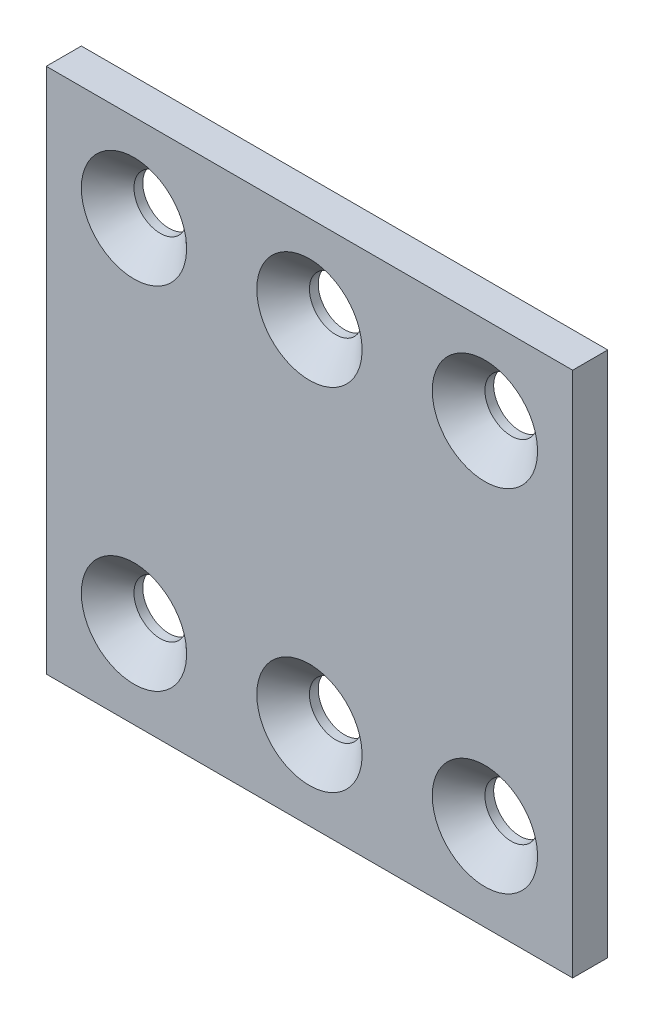
SolidWorks part; units mm, degrees
ref_plane "Front Plane" through (0, 0, 0) normal (0, 0, 1) x (1, 0, 0)
ref_plane "Top Plane" through (0, 0, 0) normal (0, 1, 0) x (1, 0, 0)
ref_plane "Right Plane" through (0, 0, 0) normal (1, 0, 0) x (0, 0, -1)
sketch "Sketch1" plane through (0, 0, 0) normal (0, 0, 1) x (1, 0, 0)
  line L1 (-30, -30) -> (30, -30)
  line L2 (-30, -30) -> (-30, 30)
  line L3 (-30, 30) -> (30, 30)
  line L4 (30, -30) -> (30, 30)
  line L5 (-30, -30) -> (30, 30) construction
  line L6 (-30, 30) -> (30, -30) construction
  point P1 (0, 0)
  point P19 (20, 20)
  point P20 (30, 30)
  point P22 (-20, 20)
  dimension "D2" = 60
  dimension "D3" = 60
extrude "Boss-Extrude1" add sketch "Sketch1" along normal mid plane 4
sketch "Sketch2" plane through (0, 0, 2) normal (0, 0, 1) x (1, 0, 0)
  line L0 (-20, -20) -> (0, -20) construction
  line L1 (0, -20) -> (20, -20) construction
  line L2 (20, -20) -> (20, 20) construction
  line L3 (20, 20) -> (0, 20) construction
  line L4 (0, 20) -> (-20, 20) construction
  line L5 (-20, 20) -> (-20, -20) construction
  line L6 (-20, -20) -> (20, 20) construction
  line L7 (0, 20) -> (0, 0) construction
  line L8 (0, 0) -> (0, -20) construction
  circle A0 centre (0, 20) radius 3
  circle A1 centre (0, -20) radius 3
  circle A2 centre (20, -20) radius 3
  circle A3 centre (-20, -20) radius 3
  circle A4 centre (-20, 20) radius 3
  circle A5 centre (20, 20) radius 3
  point P13 (0, 0)
  dimension "D1" = 6
  dimension "D2" = 40
  dimension "D3" = 40
extrude "Cut-Extrude1" cut sketch "Sketch2" against normal through all
chamfer "Chamfer1" distance 3 angle 45 6 edges at (23, -20, 2) (3, -20, 2) (-17, -20, 2) (23, 20, 2) (3, 20, 2) (-17, 20, 2)
fillet "Fillet1" [suppressed] radius 1
